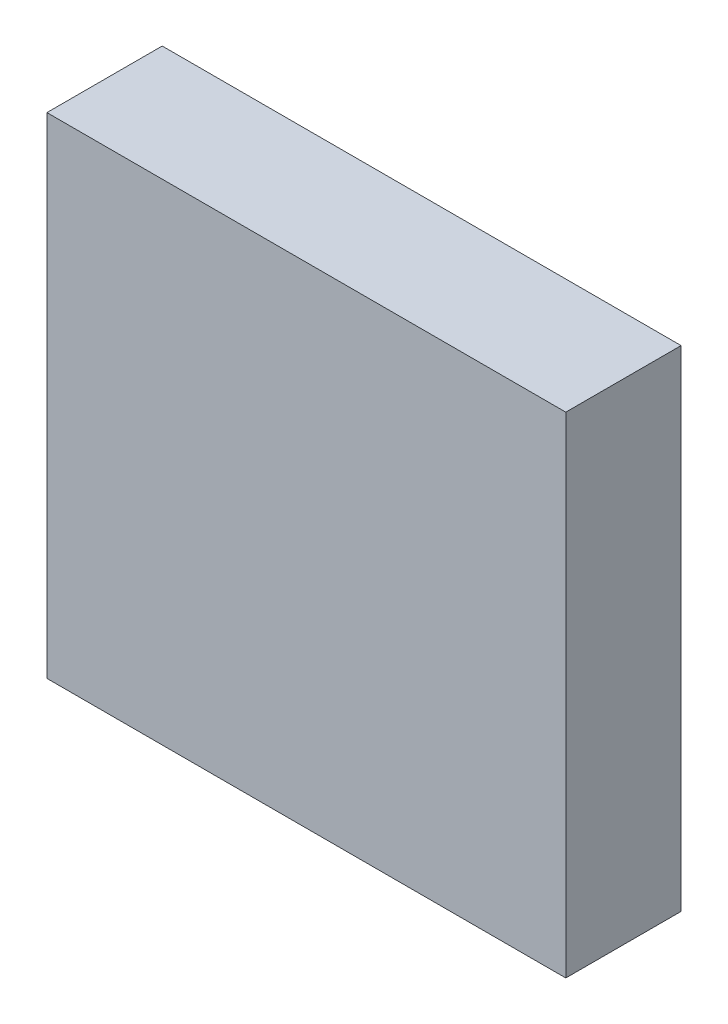
SolidWorks part; units mm, degrees
ref_plane "Front Plane" through (0, 0, 0) normal (0, 0, 1) x (1, 0, 0)
ref_plane "Top Plane" through (0, 0, 0) normal (0, 1, 0) x (1, 0, 0)
ref_plane "Right Plane" through (0, 0, 0) normal (1, 0, 0) x (0, 0, -1)
sketch "Sketch1" plane through (0, 0, 0) normal (0, 0, 1) x (1, 0, 0)
  line L1 (61.9278, 20.6028) -> (151.9278, 20.6028)
  line L2 (61.9278, 20.6028) -> (61.9278, -64.3972)
  line L3 (61.9278, -64.3972) -> (151.9278, -64.3972)
  line L4 (151.9278, 20.6028) -> (151.9278, -64.3972)
  dimension "D1" = 90
  dimension "D2" = 85
extrude "Boss-Extrude1" add sketch "Sketch1" along normal blind 20 contours L1 L4 L3 L2
